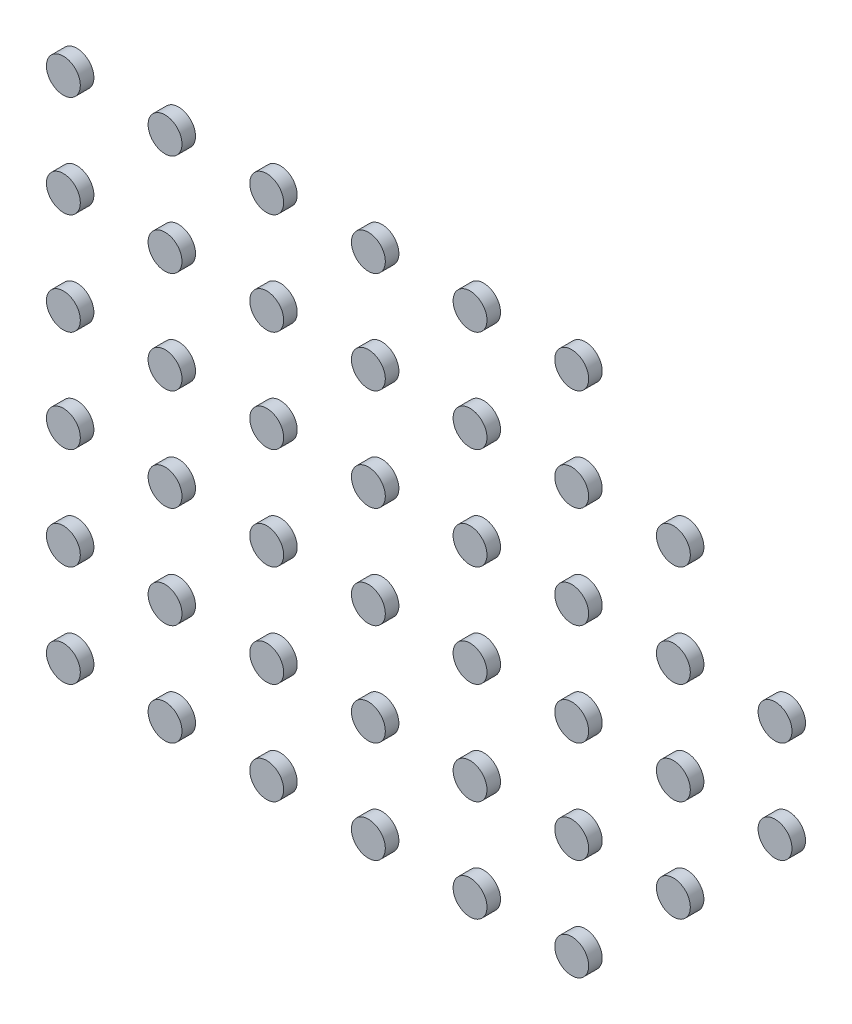
SolidWorks part; units mm, degrees
ref_plane "前视基准面" through (0, 0, 0) normal (0, 0, 1) x (1, 0, 0)
ref_plane "上视基准面" through (0, 0, 0) normal (0, 1, 0) x (1, 0, 0)
ref_plane "右视基准面" through (0, 0, 0) normal (1, 0, 0) x (0, 0, -1)
other "Configuration Table"
sketch "草图1" plane through (0, 0, 0) normal (0, 0, 1) x (1, 0, 0)
  circle A0 centre (-10.5, -7.5) radius 0.5
  circle A1 centre (-10.5, -4.5) radius 0.5
  circle A2 centre (-10.5, -1.5) radius 0.5
  circle A3 centre (-10.5, 4.5) radius 0.5
  circle A4 centre (-7.5, 4.5) radius 0.5
  circle A5 centre (-7.5, -1.5) radius 0.5
  circle A6 centre (-7.5, -4.5) radius 0.5
  circle A7 centre (-7.5, -7.5) radius 0.5
  circle A8 centre (-4.5, -7.5) radius 0.5
  circle A9 centre (-4.5, -4.5) radius 0.5
  circle A10 centre (-4.5, 1.5) radius 0.5
  circle A11 centre (-4.5, 4.5) radius 0.5
  circle A12 centre (-1.5, 4.5) radius 0.5
  circle A13 centre (-1.5, 1.5) radius 0.5
  circle A14 centre (1.5, -1.5) radius 0.5
  circle A15 centre (-1.5, -1.5) radius 0.5
  circle A16 centre (-1.5, -4.5) radius 0.5
  circle A17 centre (-1.5, -7.5) radius 0.5
  circle A18 centre (1.5, -7.5) radius 0.5
  circle A19 centre (1.5, -4.5) radius 0.5
  circle A20 centre (1.5, 1.5) radius 0.5
  circle A21 centre (1.5, 4.5) radius 0.5
  circle A22 centre (4.5, 4.5) radius 0.5
  circle A23 centre (4.5, 1.5) radius 0.5
  circle A24 centre (4.5, -1.5) radius 0.5
  circle A25 centre (4.5, -4.5) radius 0.5
  circle A26 centre (4.5, -7.5) radius 0.5
  circle A27 centre (7.5, -4.5) radius 0.5
  circle A28 centre (7.5, 1.5) radius 0.5
  circle A29 centre (7.5, -1.5) radius 0.5
  circle A30 centre (10.5, -1.5) radius 0.5
  circle A31 centre (10.5, 1.5) radius 0.5
  circle A32 centre (7.5, 4.5) radius 0.5
  circle A33 centre (4.5, 7.5) radius 0.5
  circle A34 centre (1.5, 7.5) radius 0.5
  circle A35 centre (-1.5, 7.5) radius 0.5
  circle A36 centre (-4.5, 7.5) radius 0.5
  circle A37 centre (-7.5, 7.5) radius 0.5
  circle A38 centre (-10.5, 7.5) radius 0.5
  circle A39 centre (-4.5, -1.5) radius 0.5
  circle A40 centre (-1.5, -1.5) radius 0.5
  circle A41 centre (-7.5, 1.5) radius 0.5
  circle A42 centre (-10.5, 1.5) radius 0.5
extrude "凸台-拉伸1" add sketch "草图1" along normal blind 0.4 contours A10 | A13 | A20 | A23 | A28 | A31 | A30 | A29 | A38 | A35 | A34 | A33 | A42 | A3 | A2 | A1 | A0 | A7 | A6 | A5 | A41 | A4 | A11 | A12 | A21 | A32 | A14 | A15 | A39 | A9 | A16 | A8 | A17 | A18 | A26 | A25 | A27 | A24 | A37 | A36 | A22 | A19
